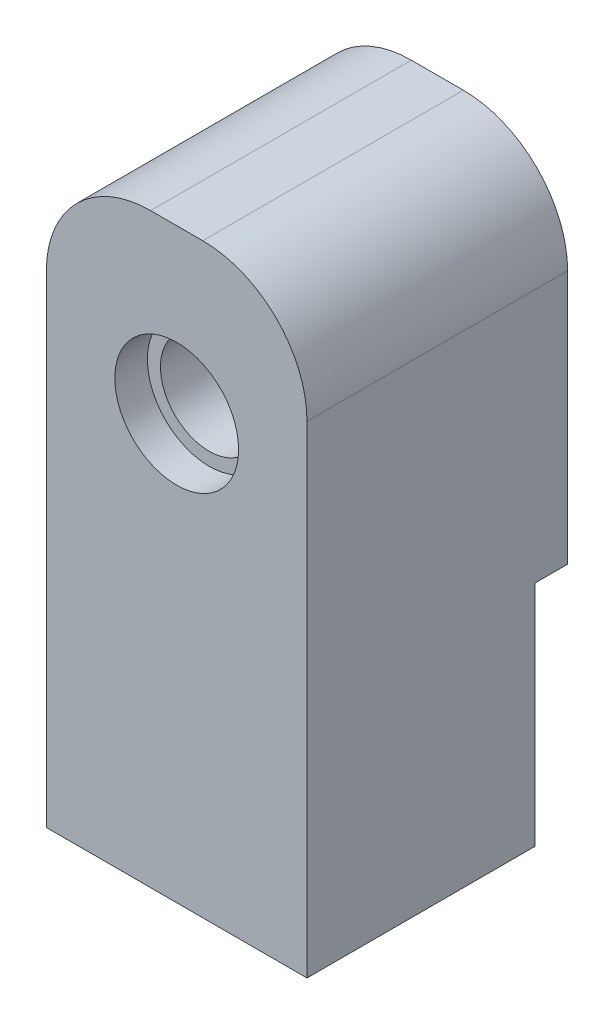
SolidWorks part; units mm, degrees
material "Plain Carbon Steel"
ref_plane "Front Plane" through (0, 0, 0) normal (0, 0, 1) x (1, 0, 0)
ref_plane "Top Plane" through (0, 0, 0) normal (0, 1, 0) x (1, 0, 0)
ref_plane "Right Plane" through (0, 0, 0) normal (1, 0, 0) x (0, 0, -1)
sketch "Sketch1" plane through (0, 0, 0) normal (1, 0, 0) x (0, 0, -1)
  line L0 (-16.5758, 0) -> (-16.5758, 57.15)
  line L1 (55, 0) -> (-55, 0) construction
  line L2 (-16.5758, 57.15) -> (8.8242, 57.15)
  line L3 (8.8242, 57.15) -> (8.8242, 22.225)
  line L4 (8.8242, 22.225) -> (5.6492, 22.225)
  line L5 (5.6492, 22.225) -> (5.6492, 0)
  line L6 (5.6492, 0) -> (-16.5758, 0)
  dimension "D1" = 22.225
  dimension "D2" = 25.4
  dimension "D3" = 22.225
  dimension "D4" = 57.15
extrude "Boss-Extrude1" add sketch "Sketch1" along normal mid plane 25.4
sketch "Sketch2" plane through (0, 0, 16.5758) normal (0, 0, 1) x (1, 0, 0)
  line L0 (0, -13.97) -> (0, 13.97) construction
  line L1 (12.7, 57.15) -> (-12.7, 57.15) construction
  circle A0 centre (0, 41.275) radius 6.0325
  dimension "D2" = 12.065
  dimension "D1" = 15.875
extrude "Cut-Extrude1" cut sketch "Sketch2" against normal blind 3.175
sketch "Sketch3" plane through (0, 0, 13.4008) normal (0, 0, 1) x (1, 0, 0)
  circle A0 centre (0, 41.275) radius 4.7625
  circle A1 centre (0, 41.275) radius 6.0325 construction
  dimension "D1" = 9.525
extrude "Cut-Extrude2" cut sketch "Sketch3" against normal through all
fillet "Fillet1" radius 10.16 2 edges at (12.7, 57.15, 3.8758) (-12.7, 57.15, 3.8758)
sketch "Sketch4" plane through (0, 0, 0) normal (0, -1, 0) x (1, 0, 0)
  line L0 (0, 27.3524) -> (0, -18.9587) construction
  line L1 (0, -13.97) -> (0, 13.97) construction
  line L2 (-30.2587, 3.8758) -> (37.081, 3.8758) construction
  line L3 (12.7, 16.5758) -> (-12.7, 16.5758) construction
  line L4 (12.7, -8.8242) -> (-12.7, -8.8242) construction
  line L5 (-12.7, 16.5758) -> (-12.7, -5.6492) construction
  line L6 (12.7, 16.5758) -> (12.7, -5.6492) construction
  circle A0 centre (0, 3.8758) radius 6.35
  point P15 (0, 3.8758)
  dimension "D1" = 12.7
extrude "Cut-Extrude3" cut sketch "Sketch4" against normal blind 30.1752
